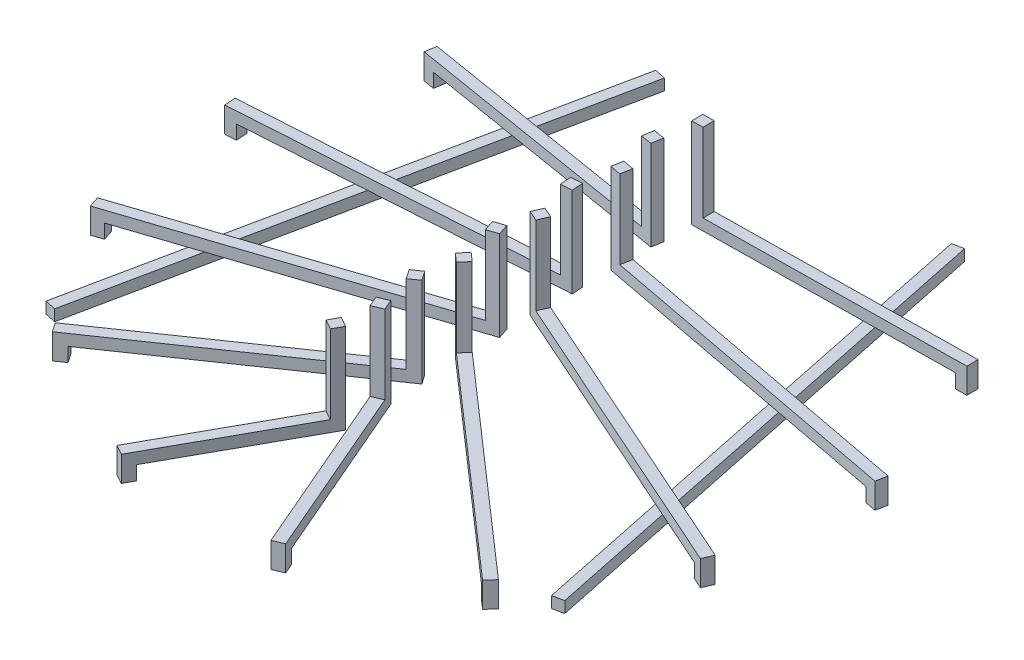
SolidWorks part; units mm, degrees
material "3.0517 (EN-AW 3003)"
ref_plane "Front Plane" through (0, 0, 0) normal (0, 0, 1) x (1, 0, 0)
ref_plane "Top Plane" through (0, 0, 0) normal (0, 1, 0) x (1, 0, 0)
ref_plane "Right Plane" through (0, 0, 0) normal (1, 0, 0) x (0, 0, -1)
sketch "Sketch2" plane through (0, 0, 0) normal (0, 1, 0) x (1, 0, 0)
  line L0 (0, -0.2556) -> (-5.3763, -2.039)
  line L1 (0, 3.2) -> (4.7322, 3.2664)
  line L2 (0, -1.6778) -> (-3.813, -4.3039)
  line L3 (0, -2.3889) -> (1.3761, -5.5829)
  line L4 (-1.5, 3.3) -> (1.5, 3.3) construction
  line L5 (-1.5, 3.1) -> (1.5, 3.1) construction
  line L6 (-1.5, 3.3) -> (1.5, 3.3) construction
  line L7 (-1.5, 3.1) -> (1.5, 3.1) construction
  line L8 (-1.5, 2.5889) -> (1.5, 2.5889) construction
  line L9 (-1.5, 2.3889) -> (1.5, 2.3889) construction
  line L10 (1.5, 1.8778) -> (-1.5, 1.8778) construction
  line L11 (-1.5, 1.6778) -> (1.5, 1.6778) construction
  line L12 (-1.5, 1.1667) -> (1.5, 1.1667) construction
  line L13 (-1.5, 0.9667) -> (1.5, 0.9667) construction
  line L14 (1.5, 0.4556) -> (-1.5, 0.4556) construction
  line L15 (-1.5, 0.2556) -> (1.5, 0.2556) construction
  line L16 (-1.5, -0.2556) -> (1.5, -0.2556) construction
  line L17 (-1.5, -0.4556) -> (1.5, -0.4556) construction
  line L18 (1.5, -0.9667) -> (-1.5, -0.9667) construction
  line L19 (1.5, -1.1667) -> (-1.5, -1.1667) construction
  line L20 (-1.5, -1.6778) -> (1.5, -1.6778) construction
  line L21 (1.5, -1.8778) -> (-1.5, -1.8778) construction
  line L22 (-1.5, -2.3889) -> (1.5, -2.3889) construction
  line L23 (1.5, -2.5889) -> (-1.5, -2.5889) construction
  line L24 (1.5, -3.1) -> (-1.5, -3.1) construction
  line L25 (1.5, -3.3) -> (-1.5, -3.3) construction
  line L26 (-1.5, 2.5889) -> (1.5, 2.5889) construction
  line L27 (-1.5, 2.3889) -> (1.5, 2.3889) construction
  line L28 (1.5, 1.8778) -> (-1.5, 1.8778) construction
  line L29 (-1.5, 1.6778) -> (1.5, 1.6778) construction
  line L30 (-1.5, 1.1667) -> (1.5, 1.1667) construction
  line L31 (-1.5, 0.9667) -> (1.5, 0.9667) construction
  line L32 (1.5, 0.4556) -> (-1.5, 0.4556) construction
  line L33 (-1.5, 0.2556) -> (1.5, 0.2556) construction
  line L34 (-1.5, -0.2556) -> (1.5, -0.2556) construction
  line L35 (-1.5, -0.4556) -> (1.5, -0.4556) construction
  line L36 (1.5, -0.9667) -> (-1.5, -0.9667) construction
  line L37 (1.5, -1.1667) -> (-1.5, -1.1667) construction
  line L38 (-1.5, -1.6778) -> (1.5, -1.6778) construction
  line L39 (1.5, -1.8778) -> (-1.5, -1.8778) construction
  line L40 (-1.5, -2.3889) -> (1.5, -2.3889) construction
  line L41 (1.5, -2.5889) -> (-1.5, -2.5889) construction
  line L42 (1.5, -3.1) -> (-1.5, -3.1) construction
  line L43 (1.5, -3.3) -> (-1.5, -3.3) construction
  line L44 (0, 3.3) -> (0, 3.1) construction
  line L45 (0, 2.5889) -> (0, 2.3889) construction
  line L46 (0, 1.8778) -> (0, 1.6778) construction
  line L47 (0, 1.1667) -> (0, 0.9667) construction
  line L48 (0, 0.4556) -> (0, 0.2556) construction
  line L49 (0, -0.2556) -> (0, -0.4556) construction
  line L50 (0, -0.9667) -> (0, -1.1667) construction
  line L51 (0, -1.6778) -> (0, -1.8778) construction
  line L52 (0, -2.3889) -> (0, -2.5889) construction
  line L53 (0, -3.1) -> (0, -3.3) construction
  line L54 (0, 1.7778) -> (5.7081, 0.6931)
  line L55 (0, 0.3556) -> (5.3763, -2.039)
  line L56 (0, -0.9667) -> (3.813, -4.3039)
  line L57 (0, -3.1) -> (-1.3761, -5.5829)
  line L58 (0, 2.4889) -> (-4.7322, 3.2664)
  line L59 (0, 1.0667) -> (-5.7081, 0.6931)
  circle A0 centre (5.7081, 0.6931) radius 0.25 construction
  circle A1 centre (5.7081, 0.6931) radius 0.25 construction
  circle A2 centre (-5.3763, -2.039) radius 0.25 construction
  circle A3 centre (-5.3763, -2.039) radius 0.25 construction
  circle A5 centre (4.7322, 3.2664) radius 0.25
  circle A6 centre (4.7322, 3.2664) radius 0.25 construction
  circle A7 centre (5.3763, -2.039) radius 0.25
  circle A8 centre (5.3763, -2.039) radius 0.25 construction
  circle A9 centre (3.813, -4.3039) radius 0.25
  circle A10 centre (3.813, -4.3039) radius 0.25 construction
  circle A11 centre (1.3761, -5.5829) radius 0.25
  circle A12 centre (1.3761, -5.5829) radius 0.25 construction
  circle A13 centre (-1.3761, -5.5829) radius 0.25
  circle A14 centre (-1.3761, -5.5829) radius 0.25 construction
  circle A15 centre (-3.813, -4.3039) radius 0.25
  circle A16 centre (-3.813, -4.3039) radius 0.25 construction
  circle A17 centre (-5.7081, 0.6931) radius 0.25
  circle A18 centre (-5.7081, 0.6931) radius 0.25 construction
  circle A19 centre (-4.7322, 3.2664) radius 0.25
  circle A20 centre (-4.7322, 3.2664) radius 0.25 construction
  circle A21 centre (-2.6722, 5.0914) radius 0.25
  circle A22 centre (-2.6722, 5.0914) radius 0.25 construction
  circle A23 centre (0, 5.75) radius 0.25
  circle A24 centre (0, 5.75) radius 0.25 construction
  circle A25 centre (2.6722, 5.0914) radius 0.25
  circle A26 centre (2.6722, 5.0914) radius 0.25 construction
  dimension "D1" = 0
  dimension "D2" = 0
  dimension "D3" = 0
  dimension "D4" = 0
  dimension "D5" = 0
  dimension "D6" = 0
  dimension "D7" = 0
  dimension "D8" = 0
  dimension "D9" = 0
  dimension "D10" = 0
  dimension "D11" = 0
extrude "Extrude-Thin1" add sketch "Sketch2" along normal blind 0.2 thin contours L55
sketch "Sketch3" plane through (0, 0.2, 0) normal (0, 1, 0) x (1, 0, 0)
  line L1 (-0.0014, 3.3) -> (0.0014, 3.1)
  line L2 (-0.0014, 3.3) -> (0.1986, 3.3028)
  line L3 (0.0014, 3.1) -> (0.2014, 3.1028)
  line L5 (0.0162, 2.5876) -> (-0.1811, 2.62)
  line L6 (0.0162, 2.5876) -> (-0.0162, 2.3902)
  line L7 (-0.1811, 2.62) -> (-0.2136, 2.4226)
  line L8 (-0.0162, 2.3902) -> (-0.2136, 2.4226)
  line L9 (0.0162, 2.5876) -> (-4.7159, 3.365) construction
  line L10 (0.0187, 1.876) -> (-0.0187, 1.6795)
  line L11 (0.0187, 1.876) -> (0.2152, 1.8387)
  line L12 (-0.0187, 1.6795) -> (0.1778, 1.6422)
  line L13 (0.2152, 1.8387) -> (0.1778, 1.6422)
  line L14 (-0.0065, 1.1665) -> (0.0065, 0.9669)
  line L15 (-0.0065, 1.1665) -> (-0.2061, 1.1534)
  line L16 (0.0065, 0.9669) -> (-0.193, 0.9538)
  line L17 (-0.2061, 1.1534) -> (-0.193, 0.9538)
  line L18 (0.0407, 0.4469) -> (-0.0407, 0.2642)
  line L19 (0.0407, 0.4469) -> (0.2234, 0.3655)
  line L20 (-0.0407, 0.2642) -> (0.142, 0.1828)
  line L21 (0.2234, 0.3655) -> (0.142, 0.1828)
  line L22 (-0.0315, -0.1606) -> (0.0315, -0.3505)
  line L23 (-0.0315, -0.1606) -> (-0.2213, -0.2236)
  line L24 (0.0315, -0.3505) -> (-0.1583, -0.4134)
  line L25 (-0.2213, -0.2236) -> (-0.1583, -0.4134)
  line L26 (0.0659, -0.8914) -> (-0.0659, -1.0419)
  line L27 (0.0659, -0.8914) -> (0.2164, -1.0231)
  line L28 (-0.0659, -1.0419) -> (0.0846, -1.1736)
  line L29 (0.2164, -1.0231) -> (0.0846, -1.1736)
  line L30 (-0.0567, -1.5954) -> (0.0567, -1.7601)
  line L31 (-0.0567, -1.5954) -> (-0.2214, -1.7089)
  line L32 (0.0567, -1.7601) -> (-0.108, -1.8736)
  line L33 (-0.2214, -1.7089) -> (-0.108, -1.8736)
  line L34 (0.0918, -2.3493) -> (-0.0918, -2.4285)
  line L35 (0.0918, -2.3493) -> (0.171, -2.533)
  line L36 (-0.0918, -2.4285) -> (-0.0127, -2.6121)
  line L37 (0.171, -2.533) -> (-0.0127, -2.6121)
  line L38 (-0.0875, -3.0515) -> (0.0875, -3.1485)
  line L39 (-0.0875, -3.0515) -> (-0.1844, -3.2265)
  line L40 (0.0875, -3.1485) -> (-0.0095, -3.3234)
  line L41 (-0.1844, -3.2265) -> (-0.0095, -3.3234)
  line L42 (0.1986, 3.3028) -> (0.2014, 3.1028)
extrude "Boss-Extrude1" add sketch "Sketch3" along normal blind 1.4
sketch "Sketch4" plane through (0, 0, 0) normal (0, -1, 0) x (1, 0, 0)
  line L0 (4.7336, -3.1664) -> (0.0014, -3.1) construction
  line L1 (0.0014, -3.1) -> (-0.0014, -3.3) construction
  line L2 (-0.0014, -3.3) -> (4.7308, -3.3664) construction
  line L3 (4.7308, -3.3664) -> (4.7336, -3.1664) construction
  line L4 (5.6894, -0.5948) -> (-0.0187, -1.6795) construction
  line L5 (-0.0187, -1.6795) -> (0.0187, -1.876) construction
  line L6 (0.0187, -1.876) -> (5.7267, -0.7913) construction
  line L7 (5.7267, -0.7913) -> (5.6894, -0.5948) construction
  line L8 (-4.7159, -3.365) -> (0.0162, -2.5876) construction
  line L9 (0.0162, -2.5876) -> (-0.0162, -2.3902) construction
  line L10 (-0.0162, -2.3902) -> (-4.7484, -3.1677) construction
  line L11 (-4.7484, -3.1677) -> (-4.7159, -3.365) construction
  line L12 (-5.7146, -0.7929) -> (-0.0065, -1.1665) construction
  line L13 (-0.0065, -1.1665) -> (0.0065, -0.9669) construction
  line L14 (0.0065, -0.9669) -> (-5.7015, -0.5933) construction
  line L15 (-5.7015, -0.5933) -> (-5.7146, -0.7929) construction
  line L16 (-5.4078, 1.9441) -> (-0.0315, 0.1606) construction
  line L17 (-0.0315, 0.1606) -> (0.0315, 0.3505) construction
  line L18 (0.0315, 0.3505) -> (-5.3449, 2.1339) construction
  line L19 (-5.3449, 2.1339) -> (-5.4078, 1.9441) construction
  line L20 (5.3357, 2.1303) -> (-0.0407, -0.2642) construction
  line L21 (-0.0407, -0.2642) -> (0.0407, -0.4469) construction
  line L22 (0.0407, -0.4469) -> (5.417, 1.9476) construction
  line L23 (5.417, 1.9476) -> (5.3357, 2.1303) construction
  line L24 (3.7471, 4.3792) -> (-0.0659, 1.0419) construction
  line L25 (-0.0659, 1.0419) -> (0.0659, 0.8914) construction
  line L26 (0.0659, 0.8914) -> (3.8788, 4.2287) construction
  line L27 (3.8788, 4.2287) -> (3.7471, 4.3792) construction
  line L28 (-3.8697, 4.2216) -> (-0.0567, 1.5954) construction
  line L29 (-0.0567, 1.5954) -> (0.0567, 1.7601) construction
  line L30 (0.0567, 1.7601) -> (-3.7562, 4.3863) construction
  line L31 (-3.7562, 4.3863) -> (-3.8697, 4.2216) construction
  line L32 (1.2842, 5.6225) -> (-0.0918, 2.4285) construction
  line L33 (-0.0918, 2.4285) -> (0.0918, 2.3493) construction
  line L34 (0.0918, 2.3493) -> (1.4679, 5.5433) construction
  line L35 (1.4679, 5.5433) -> (1.2842, 5.6225) construction
  line L36 (-1.4635, 5.5344) -> (-0.0875, 3.0515) construction
  line L37 (-0.0875, 3.0515) -> (0.0875, 3.1485) construction
  line L38 (0.0875, 3.1485) -> (-1.2886, 5.6314) construction
  line L39 (-1.2886, 5.6314) -> (-1.4635, 5.5344) construction
  line L40 (4.7336, -3.1664) -> (0.0014, -3.1) construction
  line L41 (0.0014, -3.1) -> (-0.0014, -3.3) construction
  line L42 (-0.0014, -3.3) -> (4.7308, -3.3664) construction
  line L43 (4.7308, -3.3664) -> (4.7336, -3.1664) construction
  line L44 (5.6894, -0.5948) -> (-0.0187, -1.6795) construction
  line L45 (-0.0187, -1.6795) -> (0.0187, -1.876) construction
  line L46 (0.0187, -1.876) -> (5.7267, -0.7913) construction
  line L47 (5.7267, -0.7913) -> (5.6894, -0.5948) construction
  line L48 (-4.7159, -3.365) -> (0.0162, -2.5876) construction
  line L49 (0.0162, -2.5876) -> (-0.0162, -2.3902) construction
  line L50 (-0.0162, -2.3902) -> (-4.7484, -3.1677) construction
  line L51 (-4.7484, -3.1677) -> (-4.7159, -3.365) construction
  line L52 (-5.7146, -0.7929) -> (-0.0065, -1.1665) construction
  line L53 (-0.0065, -1.1665) -> (0.0065, -0.9669) construction
  line L54 (0.0065, -0.9669) -> (-5.7015, -0.5933) construction
  line L55 (-5.7015, -0.5933) -> (-5.7146, -0.7929) construction
  line L56 (-5.4078, 1.9441) -> (-0.0315, 0.1606) construction
  line L57 (-0.0315, 0.1606) -> (0.0315, 0.3505) construction
  line L58 (0.0315, 0.3505) -> (-5.3449, 2.1339) construction
  line L59 (-5.3449, 2.1339) -> (-5.4078, 1.9441) construction
  line L60 (5.3357, 2.1303) -> (-0.0407, -0.2642) construction
  line L61 (-0.0407, -0.2642) -> (0.0407, -0.4469) construction
  line L62 (0.0407, -0.4469) -> (5.417, 1.9476) construction
  line L63 (5.417, 1.9476) -> (5.3357, 2.1303) construction
  line L64 (3.7471, 4.3792) -> (-0.0659, 1.0419) construction
  line L65 (-0.0659, 1.0419) -> (0.0659, 0.8914) construction
  line L66 (0.0659, 0.8914) -> (3.8788, 4.2287) construction
  line L67 (3.8788, 4.2287) -> (3.7471, 4.3792) construction
  line L68 (-3.8697, 4.2216) -> (-0.0567, 1.5954) construction
  line L69 (-0.0567, 1.5954) -> (0.0567, 1.7601) construction
  line L70 (0.0567, 1.7601) -> (-3.7562, 4.3863) construction
  line L71 (-3.7562, 4.3863) -> (-3.8697, 4.2216) construction
  line L72 (1.2842, 5.6225) -> (-0.0918, 2.4285) construction
  line L73 (-0.0918, 2.4285) -> (0.0918, 2.3493) construction
  line L74 (0.0918, 2.3493) -> (1.4679, 5.5433) construction
  line L75 (1.4679, 5.5433) -> (1.2842, 5.6225) construction
  line L76 (-1.4635, 5.5344) -> (-0.0875, 3.0515) construction
  line L77 (-0.0875, 3.0515) -> (0.0875, 3.1485) construction
  line L78 (0.0875, 3.1485) -> (-1.2886, 5.6314) construction
  line L79 (-1.2886, 5.6314) -> (-1.4635, 5.5344) construction
  line L80 (4.6336, -3.165) -> (4.6308, -3.365)
  line L81 (4.6336, -3.165) -> (4.8335, -3.1678)
  line L82 (4.6308, -3.365) -> (4.8307, -3.3678)
  line L83 (4.8335, -3.1678) -> (4.8307, -3.3678)
  line L84 (4.6336, -3.165) -> (4.8307, -3.3678) construction
  line L85 (4.6308, -3.365) -> (4.8335, -3.1678) construction
  line L86 (0.0014, -3.1) -> (4.7336, -3.1664) construction
  line L87 (5.7876, -0.5762) -> (5.825, -0.7727)
  line L88 (5.7876, -0.5762) -> (5.5912, -0.6135)
  line L89 (5.825, -0.7727) -> (5.6285, -0.81)
  line L90 (5.5912, -0.6135) -> (5.6285, -0.81)
  line L91 (5.7876, -0.5762) -> (5.6285, -0.81) construction
  line L92 (5.825, -0.7727) -> (5.5912, -0.6135) construction
  line L93 (-0.0187, -1.6795) -> (5.6894, -0.5948) construction
  line L94 (5.427, 2.171) -> (5.5084, 1.9883)
  line L95 (5.427, 2.171) -> (5.2443, 2.0896)
  line L96 (5.5084, 1.9883) -> (5.3257, 1.9069)
  line L97 (5.2443, 2.0896) -> (5.3257, 1.9069)
  line L98 (5.427, 2.171) -> (5.3257, 1.9069) construction
  line L99 (5.5084, 1.9883) -> (5.2443, 2.0896) construction
  line L100 (-0.0407, -0.2642) -> (5.3357, 2.1303) construction
  line L101 (3.8223, 4.445) -> (3.9541, 4.2945)
  line L102 (3.8223, 4.445) -> (3.6718, 4.3133)
  line L103 (3.9541, 4.2945) -> (3.8036, 4.1628)
  line L104 (3.6718, 4.3133) -> (3.8036, 4.1628)
  line L105 (3.8223, 4.445) -> (3.8036, 4.1628) construction
  line L106 (3.9541, 4.2945) -> (3.6718, 4.3133) construction
  line L107 (-0.0659, 1.0419) -> (3.7471, 4.3792) construction
  line L108 (1.3238, 5.7143) -> (1.5075, 5.6352)
  line L109 (1.3238, 5.7143) -> (1.2447, 5.5306)
  line L110 (1.5075, 5.6352) -> (1.4283, 5.4515)
  line L111 (1.2447, 5.5306) -> (1.4283, 5.4515)
  line L112 (1.3238, 5.7143) -> (1.4283, 5.4515) construction
  line L113 (1.5075, 5.6352) -> (1.2447, 5.5306) construction
  line L114 (-0.0918, 2.4285) -> (1.2842, 5.6225) construction
  line L115 (-1.512, 5.6219) -> (-1.3371, 5.7189)
  line L116 (-1.512, 5.6219) -> (-1.4151, 5.447)
  line L117 (-1.3371, 5.7189) -> (-1.2401, 5.5439)
  line L118 (-1.4151, 5.447) -> (-1.2401, 5.5439)
  line L119 (-1.512, 5.6219) -> (-1.2401, 5.5439) construction
  line L120 (-1.3371, 5.7189) -> (-1.4151, 5.447) construction
  line L121 (-0.0875, 3.0515) -> (-1.4635, 5.5344) construction
  line L122 (-3.952, 4.2783) -> (-3.8386, 4.443)
  line L123 (-3.952, 4.2783) -> (-3.7873, 4.1649)
  line L124 (-3.8386, 4.443) -> (-3.6739, 4.3296)
  line L125 (-3.7873, 4.1649) -> (-3.6739, 4.3296)
  line L126 (-3.952, 4.2783) -> (-3.6739, 4.3296) construction
  line L127 (-3.8386, 4.443) -> (-3.7873, 4.1649) construction
  line L128 (-0.0567, 1.5954) -> (-3.8697, 4.2216) construction
  line L129 (-5.4398, 2.1654) -> (-5.5027, 1.9755)
  line L130 (-5.4398, 2.1654) -> (-5.2499, 2.1024)
  line L131 (-5.5027, 1.9755) -> (-5.3129, 1.9126)
  line L132 (-5.2499, 2.1024) -> (-5.3129, 1.9126)
  line L133 (-5.4398, 2.1654) -> (-5.3129, 1.9126) construction
  line L134 (-5.5027, 1.9755) -> (-5.2499, 2.1024) construction
  line L135 (-0.0315, 0.1606) -> (-5.4078, 1.9441) construction
  line L136 (-5.8144, -0.7863) -> (-5.8013, -0.5868)
  line L137 (-5.8144, -0.7863) -> (-5.6148, -0.7994)
  line L138 (-5.8013, -0.5868) -> (-5.6018, -0.5998)
  line L139 (-5.6148, -0.7994) -> (-5.6018, -0.5998)
  line L140 (-5.8144, -0.7863) -> (-5.6018, -0.5998) construction
  line L141 (-5.8013, -0.5868) -> (-5.6148, -0.7994) construction
  line L142 (-0.0065, -1.1665) -> (-5.7146, -0.7929) construction
  line L143 (-4.847, -3.1839) -> (-4.8146, -3.3813)
  line L144 (-4.847, -3.1839) -> (-4.6497, -3.1515)
  line L145 (-4.8146, -3.3813) -> (-4.6173, -3.3488)
  line L146 (-4.6497, -3.1515) -> (-4.6173, -3.3488)
  line L147 (-4.847, -3.1839) -> (-4.6173, -3.3488) construction
  line L148 (-4.8146, -3.3813) -> (-4.6497, -3.1515) construction
  line L149 (0.0162, -2.5876) -> (-4.7159, -3.365) construction
  point P38 (4.7322, -3.2664)
  point P41 (4.7322, -3.2664)
  point P44 (5.7081, -0.6931)
  point P45 (5.7081, -0.6931)
  point P52 (5.3763, 2.039)
  point P53 (5.3763, 2.039)
  point P60 (3.813, 4.3039)
  point P61 (3.813, 4.3039)
  point P68 (1.3761, 5.5829)
  point P69 (1.3761, 5.5829)
  point P76 (-1.3761, 5.5829)
  point P77 (-1.3761, 5.5829)
  point P84 (-3.813, 4.3039)
  point P85 (-3.813, 4.3039)
  point P92 (-5.3763, 2.039)
  point P93 (-5.3763, 2.039)
  point P100 (-5.7081, -0.6931)
  point P101 (-5.7081, -0.6931)
  point P108 (-4.7322, -3.2664)
  point P109 (-4.7322, -3.2664)
extrude "Boss-Extrude3" add sketch "Sketch4" along normal blind 0.25 and the other way up to surface
ref_plane "Plane1" through (0, -0.25, 0) normal (0, 1, 0) x (1, 0, 0)
sketch "Sketch5" plane through (0, -0.25, 0) normal (0, 1, 0) x (1, 0, 0)
  line L0 (2.6722, 5.0914) -> (4.5, -3.7) construction
  line L1 (-2.6722, 5.0914) -> (-4.5, -3.7) construction
  line L2 (4.4224, -3.8183) -> (2.5539, 5.1689)
  line L3 (4.4224, -3.8183) -> (4.6183, -3.7776)
  line L4 (2.5539, 5.1689) -> (2.7497, 5.2096)
  line L5 (4.6183, -3.7776) -> (2.7497, 5.2096)
  line L6 (4.4224, -3.8183) -> (2.7497, 5.2096) construction
  line L7 (2.5539, 5.1689) -> (4.6183, -3.7776) construction
  line L8 (2.6518, 5.1893) -> (2.6722, 5.0914) construction
  line L9 (-4.6183, -3.7776) -> (-2.7497, 5.2096)
  line L10 (-4.6183, -3.7776) -> (-4.4224, -3.8183)
  line L11 (-2.7497, 5.2096) -> (-2.5539, 5.1689)
  line L12 (-4.4224, -3.8183) -> (-2.5539, 5.1689)
  line L13 (-4.6183, -3.7776) -> (-2.5539, 5.1689) construction
  line L14 (-2.7497, 5.2096) -> (-4.4224, -3.8183) construction
  line L15 (-2.6518, 5.1893) -> (-2.6722, 5.0914) construction
  circle A0 centre (-4.5, -3.7) radius 0.7099 construction
  circle A1 centre (-4.5, -3.7) radius 0.7099 construction
  circle A2 centre (4.5, -3.7) radius 0.7099 construction
  circle A3 centre (4.5, -3.7) radius 0.7099 construction
  circle A4 centre (-2.6722, 5.0914) radius 0.25 construction
  circle A5 centre (-2.6722, 5.0914) radius 0.25 construction
  circle A6 centre (2.6722, 5.0914) radius 0.25 construction
  circle A7 centre (2.6722, 5.0914) radius 0.25 construction
  point P13 (3.5861, 0.6957)
  point P15 (-3.5861, 0.6957)
  dimension "D1" = 0.1
  dimension "D2" = 0.2
  dimension "D3" = 0.1
  dimension "D4" = 0.1
  dimension "D5" = 0.2
  dimension "D6" = 0.1
extrude "Boss-Extrude4" add sketch "Sketch5" along normal blind 0.2 separate body
